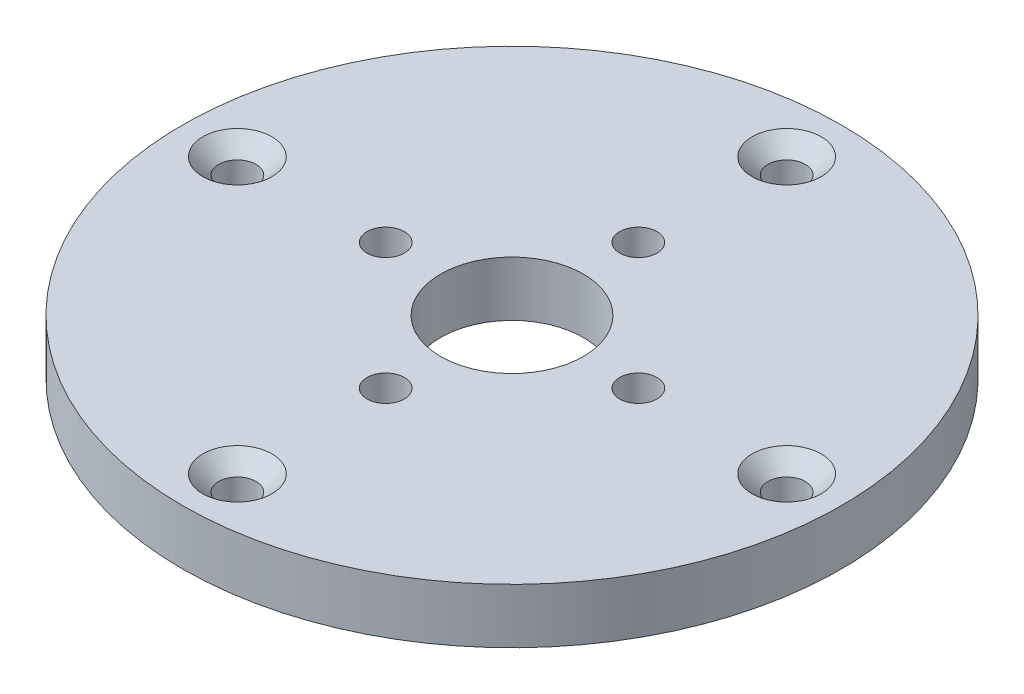
SolidWorks part; units mm, degrees
ref_plane "Front Plane" through (0, 0, 0) normal (0, 0, 1) x (1, 0, 0)
ref_plane "Top Plane" through (0, 0, 0) normal (0, 1, 0) x (1, 0, 0)
ref_plane "Right Plane" through (0, 0, 0) normal (1, 0, 0) x (0, 0, -1)
sketch "Sketch1" plane through (0, 0, 0) normal (0, 1, 0) x (1, 0, 0)
  circle A0 centre (0, 0) radius 25 construction
  circle A1 centre (0, 0) radius 11.5 construction
  circle A2 centre (0, 0) radius 30
  circle A3 centre (0, 0) radius 6.5
  dimension "D1" = 50
  dimension "D2" = 23
  dimension "D3" = 5
  dimension "D4" = 5
extrude "Boss-Extrude1" add sketch "Sketch1" along normal blind 5
hole_wizard "CSK for M3 Countersunk Flat Head Screw1" positions "Sketch2" profile "Sketch3" countersink size "M3" standard "ISO" end condition up to next
sketch "Sketch2" plane through (0, 5, 0) normal (0, 1, 0) x (1, 0, 0)
  circle A0 centre (0, 0) radius 25 construction
  point P0 (0, 25)
  point P4 (-25, 0)
  point P6 (0, -25)
  point P8 (25, 0)
sketch "Sketch3" plane through (0, 5, -25) normal (1, 0, 0) x (0, 0, 1)
  line L0 (0, 0) -> (0, 5)
  line L1 (0, 5) -> (1.7, 5)
  line L2 (1.7, 5) -> (1.7, 1.45)
  line L3 (1.7, 1.45) -> (3.15, 0)
  line L5 (3.15, 0) -> (0, 0)
  line L6 (-1.7, 1.45) -> (-3.15, 0) construction
  line L11 (0, -6.35) -> (0, 107.95) construction
  dimension "Thru Hole Dia." = 3.4
  dimension "Thru Hole Depth" = 5
  dimension "Near C'Sink Dia." = 6.3
  dimension "Near C'Sink Angle" = 90
hole_wizard "CSK for M3 Countersunk Flat Head Screw2" positions "Sketch4" profile "Sketch5" countersink size "M3" standard "ISO" end condition up to next
sketch "Sketch4" plane through (0, 0, 0) normal (0, -1, 0) x (-1, 0, 0)
  circle A0 centre (0, 0) radius 11.5 construction
  point P0 (0, 11.5)
  point P4 (-11.5, 0)
  point P6 (0, -11.5)
  point P8 (11.5, 0)
sketch "Sketch5" plane through (0, 0, -11.5) normal (1, 0, 0) x (0, 0, -1)
  line L0 (0, 0) -> (0, 5)
  line L1 (0, 5) -> (1.7, 5)
  line L2 (1.7, 5) -> (1.7, 1.45)
  line L3 (1.7, 1.45) -> (3.15, 0)
  line L5 (3.15, 0) -> (0, 0)
  line L6 (-1.7, 1.45) -> (-3.15, 0) construction
  line L11 (0, -6.35) -> (0, 107.95) construction
  dimension "Thru Hole Dia." = 3.4
  dimension "Thru Hole Depth" = 5
  dimension "Near C'Sink Dia." = 6.3
  dimension "Near C'Sink Angle" = 90
